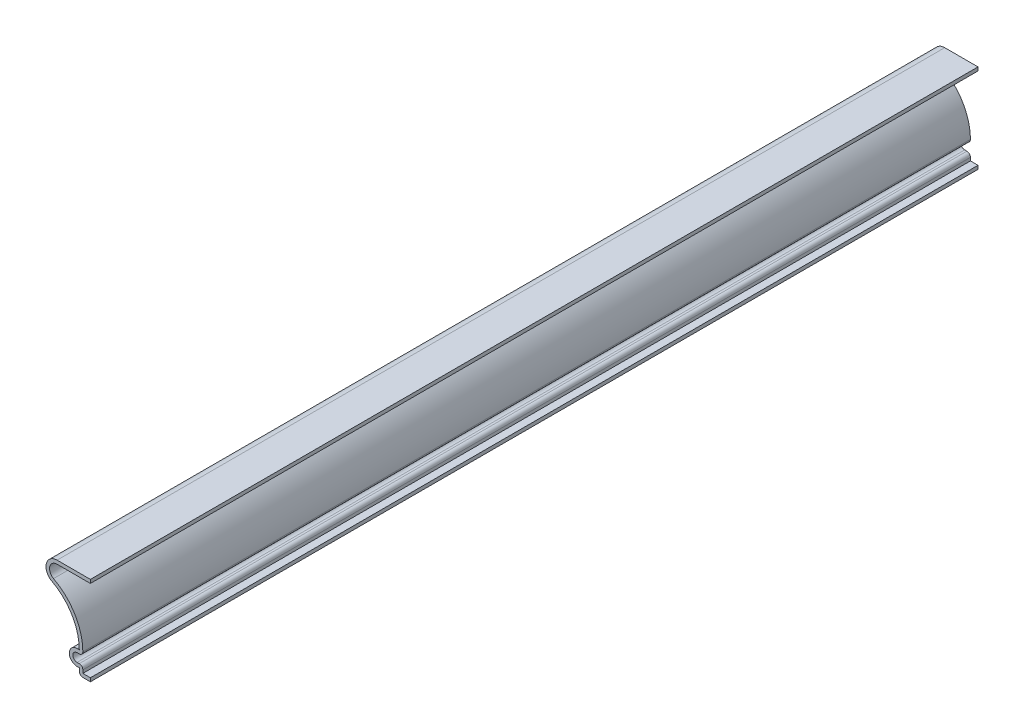
SolidWorks part; units mm, degrees
ref_plane "Front Plane" through (0, 0, 0) normal (0, 0, 1) x (1, 0, 0)
ref_plane "Top Plane" through (0, 0, 0) normal (0, 1, 0) x (1, 0, 0)
ref_plane "Right Plane" through (0, 0, 0) normal (1, 0, 0) x (0, 0, -1)
sketch "Sketch1" plane through (0, 0, 0) normal (0, 0, 1) x (1, 0, 0)
  line L0 (0, 0) -> (0, 31.75) construction
  line L1 (0, 31.75) -> (-11.9062, 31.75)
  line L2 (0, 0) -> (-3.9688, 0)
  line L3 (-3.9688, 0) -> (-3.9688, 2.3812)
  line L4 (-3.9688, 2.3812) -> (-4.7625, 2.3813)
  line L5 (-4.7625, 7.9375) -> (-3.9688, 7.9375)
  line L6 (-3.9688, 7.9375) -> (-3.9688, 32.8207) construction
  arc A0 (-11.9062, 31.75) -> (-13.7739, 24.2794) centre (-11.9062, 27.7812) ccw
  arc A1 (-4.7625, 2.3813) -> (-4.7625, 7.9375) centre (-4.7625, 5.1594) cw
  arc A2 (-13.7739, 24.2794) -> (-3.9688, 7.9375) centre (-22.4896, 7.9375) cw
  point P11 (-11.7972, 21.156)
  point P15 (0, 0)
  point P16 (-11.1393, 21.156)
  point P17 (-12.4902, 23.4499)
  point P18 (0, 0)
  point P19 (-13.8176, 24.3031)
  point P20 (-10.7876, 23.9734)
  point P21 (-10.1909, 23.9734)
  point P22 (-11.1438, 23.8864)
  dimension "D8" = 7.9375
  dimension "D1" = 3.9688
  dimension "D2" = 2.3813
  dimension "D3" = 5.5562
  dimension "D4" = 11.9062
  dimension "D5" = 31.75
  dimension "D6" = 15.875
  dimension "D7" = 0.7937
extrude "Extrude-Thin1" add sketch "Sketch1" against normal blind 317.5 thin thin type one direction reverse wall 1.27
fillet "Fillet1" radius 1.27 3 edges at (-3.9688, 0, -158.75) (-2.6987, 3.6512, -158.75) (-2.7395, 6.6675, -158.75)
